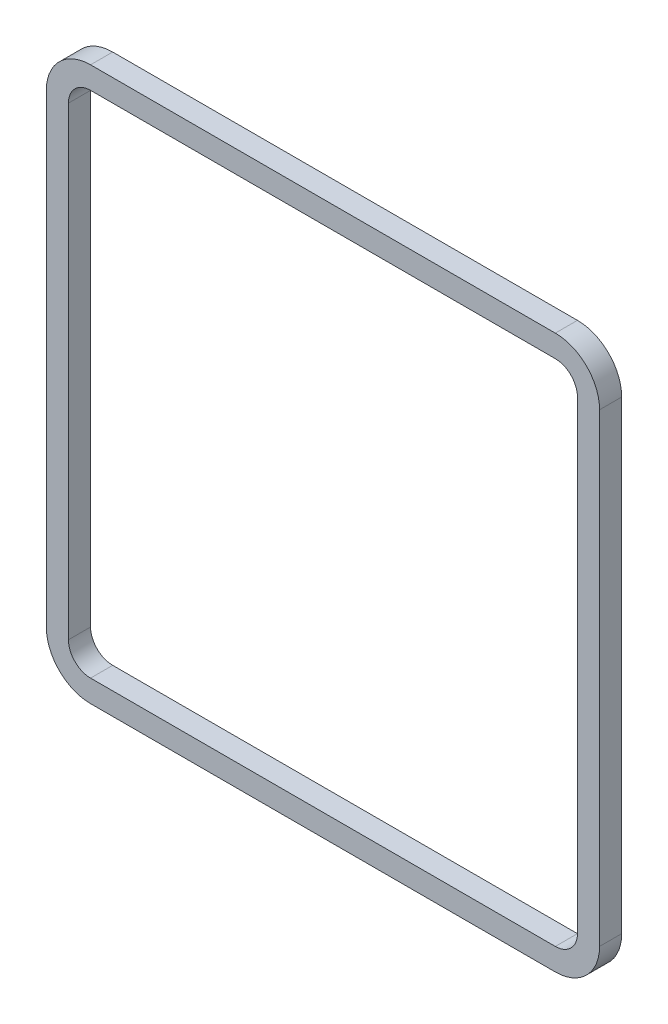
SolidWorks part; units mm, degrees
ref_plane "Front Plane" through (0, 0, 0) normal (0, 0, 1) x (1, 0, 0)
ref_plane "Top Plane" through (0, 0, 0) normal (0, 1, 0) x (1, 0, 0)
ref_plane "Right Plane" through (0, 0, 0) normal (1, 0, 0) x (0, 0, -1)
sketch "Sketch1" plane through (0, 0, 0) normal (0, 0, 1) x (1, 0, 0)
  line L0 (53.34, 58.42) -> (-53.34, 58.42)
  line L1 (53.34, 63.5) -> (-53.34, 63.5)
  line L2 (63.5, 53.34) -> (63.5, -53.34)
  line L3 (53.34, -63.5) -> (-53.34, -63.5)
  line L4 (-63.5, 53.34) -> (-63.5, -53.34)
  line L5 (63.5, 63.5) -> (-63.5, -63.5) construction
  line L6 (63.5, -63.5) -> (-63.5, 63.5) construction
  line L7 (-58.42, 53.34) -> (-58.42, -53.34)
  line L8 (53.34, -58.42) -> (-53.34, -58.42)
  line L9 (58.42, 53.34) -> (58.42, -53.34)
  arc A0 (63.5, 53.34) -> (53.34, 63.5) centre (53.34, 53.34) ccw
  arc A1 (53.34, -63.5) -> (63.5, -53.34) centre (53.34, -53.34) ccw
  arc A2 (-63.5, -53.34) -> (-53.34, -63.5) centre (-53.34, -53.34) ccw
  arc A3 (-53.34, 63.5) -> (-63.5, 53.34) centre (-53.34, 53.34) ccw
  arc A4 (-53.34, 58.42) -> (-58.42, 53.34) centre (-53.34, 53.34) ccw
  arc A5 (-58.42, -53.34) -> (-53.34, -58.42) centre (-53.34, -53.34) ccw
  arc A6 (53.34, -58.42) -> (58.42, -53.34) centre (53.34, -53.34) ccw
  arc A7 (58.42, 53.34) -> (53.34, 58.42) centre (53.34, 53.34) ccw
  point P0 (0, 0)
  dimension "D3" = 10.16
  dimension "D1" = 127
  dimension "D2" = 127
  dimension "D4" = 5.08
extrude "Boss-Extrude1" add sketch "Sketch1" along normal blind 5.08
